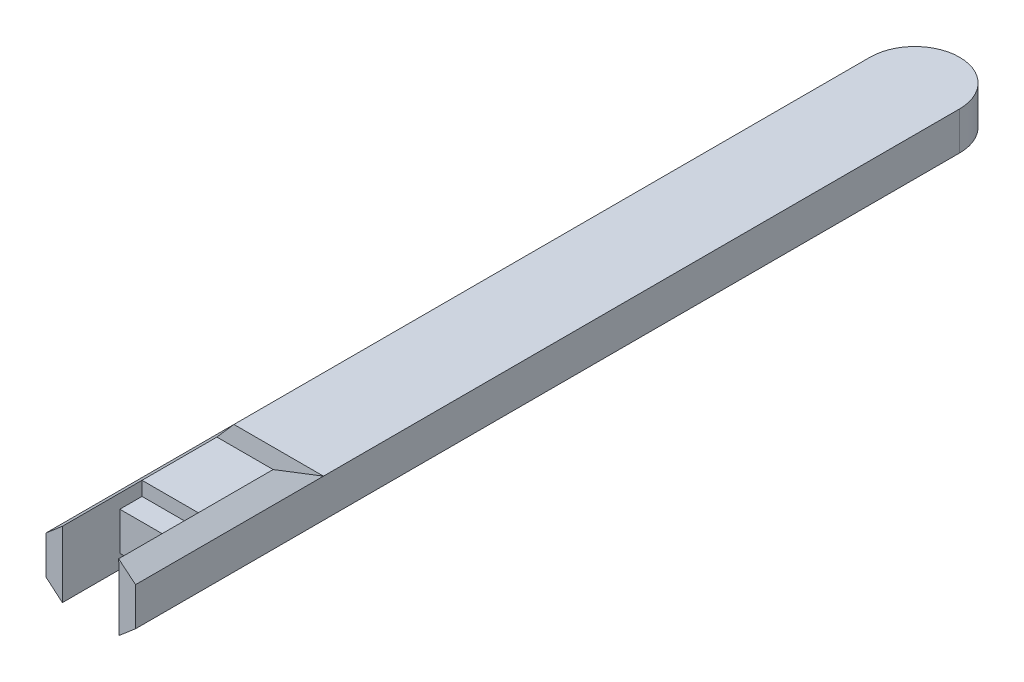
SolidWorks part; units mm, degrees
ref_plane "Front Plane" through (0, 0, 0) normal (0, 0, 1) x (1, 0, 0)
ref_plane "Top Plane" through (0, 0, 0) normal (0, 1, 0) x (1, 0, 0)
ref_plane "Right Plane" through (0, 0, 0) normal (1, 0, 0) x (0, 0, -1)
sketch "Sketch1" plane through (0, 0, 0) normal (0, 1, 0) x (1, 0, 0)
  line L1 (6.7, 61.65) -> (-6.7, 61.65)
  line L2 (6.7, 61.65) -> (6.7, -61.65)
  line L3 (6.7, -61.65) -> (-6.7, -61.65)
  line L4 (-6.7, 61.65) -> (-6.7, -61.65)
  line L5 (6.7, 61.65) -> (-6.7, -61.65) construction
  line L6 (6.7, -61.65) -> (-6.7, 61.65) construction
  arc A0 (-6.7, 61.65) -> (6.7, 61.65) centre (0, 61.65) cw
  point P0 (0, 0)
  dimension "D2" = 6.7
  dimension "D1" = 13.4
  dimension "D3" = 123.3
extrude "Boss-Extrude1" add sketch "Sketch1" along normal blind 5.72 contours L1 L4 L3 L2 | A0 L1
sketch "Sketch3" plane through (6.7, 0, 0) normal (1, 0, 0) x (0, 0, -1)
  line L0 (-49.73, 5.72) -> (-33.53, 5.72)
  line L1 (61.65, 5.72) -> (-61.65, 5.72) construction
  line L2 (-33.53, 5.72) -> (-49.73, 5.72)
  line L3 (-49.73, 7.81) -> (-49.73, 5.72)
  line L4 (-38.53, 7.81) -> (-49.73, 7.81)
  line L5 (-38.53, 7.81) -> (-33.53, 5.72)
  line M6 (61.65, 5.72) -> (-61.65, 5.72)
  dimension "D1" = 11.92
  dimension "D2" = 16.2
  dimension "D3" = 2.09
  dimension "D4" = 11.2
extrude "Boss-Extrude2" add sketch "Sketch3" against normal blind 13.4 contours L5 L4 L3 M6
sketch "Sketch4" plane through (6.7, 0, 0) normal (1, 0, 0) x (0, 0, -1)
  line L0 (-49.73, 0) -> (-33.53, 0)
  line L1 (61.65, 0) -> (-61.65, 0) construction
  line L2 (-33.53, 0) -> (-38.53, -2.09)
  line L3 (-38.53, -2.09) -> (-49.73, -2.09)
  line L4 (-49.73, -2.09) -> (-49.73, 0)
  dimension "D1" = 11.92
  dimension "D2" = 11.2
  dimension "D3" = 16.2
  dimension "D4" = 2.09
extrude "Boss-Extrude3" add sketch "Sketch4" against normal blind 13.4
sketch "Sketch5" plane through (0, 0, 0) normal (0, -1, 0) x (1, 0, 0)
  line L0 (-4.25, 61.65) -> (-4.25, 53.05)
  line L1 (6.7, 61.65) -> (-6.7, 61.65) construction
  line L2 (-4.25, 53.05) -> (4.25, 53.05)
  line L3 (4.25, 53.05) -> (4.25, 61.65)
  line L4 (4.25, 61.65) -> (-4.25, 61.65)
  line L5 (-6.7, 49.73) -> (-6.7, 61.65) construction
  dimension "D1" = 8.6
  dimension "D2" = 8.5
  dimension "D3" = 2.45
extrude "Cut-Extrude1" cut sketch "Sketch5" against normal blind 13.4
sketch "Sketch6" plane through (0, 0, 61.65) normal (0, 0, 1) x (1, 0, 0)
  line L2 (-4.25, 5.72) -> (-6.7, 5.72)
  line L3 (-6.7, 5.72) -> (-4.25, 7.81)
  line L4 (-6.7, 7.81) -> (6.7, 7.81) construction
  line L5 (-4.25, 7.81) -> (-4.25, 5.72)
extrude "Boss-Extrude4" add sketch "Sketch6" against normal blind 11.95
sketch "Sketch8" plane through (0, 0, 61.65) normal (0, 0, 1) x (1, 0, 0)
  line L0 (6.7, 5.72) -> (4.1696, 7.81)
  line L1 (-4.25, 7.81) -> (6.7, 7.81) construction
  line L2 (4.1696, 7.81) -> (4.25, 5.72)
  line L3 (4.25, 5.72) -> (6.7, 5.72)
extrude "Boss-Extrude5" add sketch "Sketch8" against normal blind 11.95
sketch "Sketch10" plane through (0, 0, 49.73) normal (0, 0, 1) x (1, 0, 0)
  line L0 (-6.7, 7.81) -> (-6.7, 5.72)
  line L1 (-6.7, 5.72) -> (-4.25, 7.81)
  line L2 (-4.25, 7.81) -> (-6.7, 7.81)
extrude "Cut-Extrude3" cut sketch "Sketch10" against normal blind 16.5
sketch "Sketch11" plane through (0, 0, 61.65) normal (0, 0, 1) x (1, 0, 0)
  line L0 (4.2455, 0) -> (4.2455, -2.09)
  line L1 (6.7, 0) -> (4.25, 0) construction
  line L2 (4.2455, -2.09) -> (6.7, 0)
  line L3 (6.7, 0) -> (4.2455, 0)
  line L4 (-6.7, -2.09) -> (6.7, -2.09) construction
  point P4 (4.2455, -2.09)
extrude "Boss-Extrude6" add sketch "Sketch11" against normal blind 11.95
sketch "Sketch13" plane through (0, 0, 49.73) normal (0, 0, 1) x (1, 0, 0)
  line L0 (6.7, 0) -> (4.2455, -2.09)
  line L1 (4.2455, -2.09) -> (6.7, -2.09)
  line L2 (6.7, -2.09) -> (6.7, 0)
extrude "Cut-Extrude6" cut sketch "Sketch13" against normal blind 16.6
sketch "Sketch14" plane through (0, 0, 49.73) normal (0, 0, 1) x (1, 0, 0)
  line L0 (4.1696, 7.81) -> (6.7, 7.81)
  line L1 (6.7, 7.81) -> (6.7, 5.72)
  line L2 (6.7, 5.72) -> (4.1696, 7.81)
extrude "Cut-Extrude7" cut sketch "Sketch14" against normal blind 16.6
sketch "Sketch15" plane through (0, 0, 61.65) normal (0, 0, 1) x (1, 0, 0)
  line L2 (-6.7, 0) -> (-4.2957, 0)
  line L3 (-6.7, 0) -> (4.2455, 0) construction
  line L5 (-6.7, 0) -> (-4.2957, 0)
  line L6 (-6.7, 0) -> (-4.25, 0)
  line L7 (-4.25, 7.81) -> (-4.25, 0) construction
  line L8 (-4.25, 0) -> (-4.25, -2.09)
  line L9 (-6.7, -2.09) -> (4.2455, -2.09) construction
  line L10 (-4.25, -2.09) -> (-6.7, 0)
  line M4 (-6.7, 0) -> (-4.25, 0)
extrude "Boss-Extrude7" add sketch "Sketch15" against normal blind 11.95 contours L10 L8 M4
sketch "Sketch16" plane through (0, 0, 49.73) normal (0, 0, 1) x (1, 0, 0)
  line L0 (-6.7, 0) -> (-6.7, -2.09)
  line L1 (-6.7, -2.09) -> (-4.25, -2.09)
  line L2 (-4.25, -2.09) -> (-6.7, 0)
extrude "Cut-Extrude8" cut sketch "Sketch16" against normal blind 16.6
